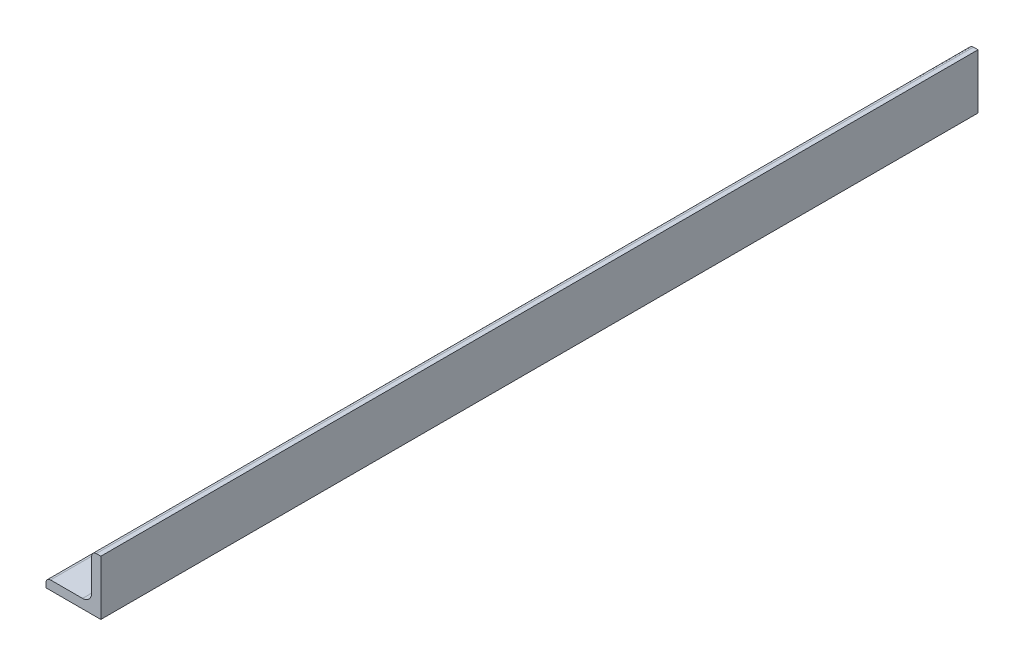
SolidWorks part; units mm, degrees
material "6061-T6 (SS)"
ref_plane "Front Plane" through (0, 0, 0) normal (0, 0, 1) x (1, 0, 0)
ref_plane "Top Plane" through (0, 0, 0) normal (0, 1, 0) x (1, 0, 0)
ref_plane "Right Plane" through (0, 0, 0) normal (1, 0, 0) x (0, 0, -1)
sketch "Sketch0" plane through (0, 0, 0) normal (0, 0, 1) x (1, 0, 0)
  line L0 (-9.525, -9.525) -> (9.525, -9.525)
  line L1 (9.525, -9.525) -> (9.525, 9.525)
  line L2 (9.525, 0) -> (0, 0) construction
  line L3 (0, 0) -> (0, -9.525) construction
  line L4 (6.35, -3.175) -> (6.35, 9.525) construction
  line L5 (3.175, -6.35) -> (-9.525, -6.35) construction
  arc A0 (6.35, -3.175) -> (3.175, -6.35) centre (3.175, -3.175) cw
  point P3 (5.4201, -5.4201)
  dimension "Inside Corner Radius" = 3.175
  dimension "Outside Height" = 19.05
  dimension "Inside Height" = 15.875
  dimension "Inside Width" = 15.875
  dimension "Wall Thickness" = 3.175
  dimension "D1" = 3.175
  dimension "Outside Width" = 19.05
sketch "Sketch1" plane through (0, 0, 0) normal (1, 0, 0) x (0, 0, -1)
  line L0 (152.4, 0) -> (-152.4, 0)
  point P4 (0, 0)
  dimension "Length" = 304.8
sketch "Sketch2" plane through (0, 0, 0) normal (0, 0, 1) x (1, 0, 0)
  line L0 (-9.525, -9.525) -> (9.525, -9.525)
  line L1 (9.525, -9.525) -> (9.525, 9.525)
  line L2 (9.525, 9.525) -> (6.35, 9.525) construction
  line L3 (6.35, 7.9375) -> (6.35, -3.175)
  line L4 (3.175, -6.35) -> (-7.9375, -6.35)
  line L5 (-9.525, -9.525) -> (-9.525, -6.35) construction
  line L6 (7.9375, 9.525) -> (9.525, 9.525)
  line L7 (-9.525, -7.9375) -> (-9.525, -9.525)
  line L8 (9.525, 0) -> (0, 0) construction
  line L9 (0, 0) -> (0, -9.525) construction
  arc A0 (6.35, 7.9375) -> (7.9375, 9.525) centre (7.9375, 7.9375) cw
  arc A1 (-9.525, -7.9375) -> (-7.9375, -6.35) centre (-7.9375, -7.9375) cw
  arc A2 (6.35, -3.175) -> (3.175, -6.35) centre (3.175, -3.175) cw
  dimension "Inside Radius" = 3.175
  dimension "Height" = 19.05
  dimension "Width" = 19.05
  dimension "Thickness" = 3.175
extrude "Boss-Extrude1" add sketch "Sketch2" along normal mid plane 304.8
sketch "Break Locations" plane through (0, 0, 0) normal (1, 0, 0) x (0, 0, -1)
  line L0 (-132.969, 0) -> (132.969, 0)
  line L1 (-152.4, -9.525) -> (-152.4, 9.525) construction
  line L2 (152.4, -9.525) -> (152.4, 9.525) construction
  point P0 (-136.2075, 0)
  point P1 (136.2075, 0)
  point P10 (0, 0)
  point P11 (132.969, 0)
  point P13 (-132.969, 0)
  dimension "D1" = 16.1925
  dimension "D2" = 16.1925
  dimension "D3" = 19.431
equation "\"D1@Break Locations\" = .85 * \"Height@Sketch2\""
equation "\"D2@Break Locations\"=\"D1@Break Locations\""
equation "\"Thickness@Sketch2\"=\"wall thickness@sketch0\""
equation "\"Height@Sketch2\"=\"outside height@sketch0\""
equation "\"Width@Sketch2\"=\"outside width@sketch0\""
equation "\"Inside Radius@Sketch2\"=\"inside corner radius@sketch0\""
equation "\"Length@Boss-Extrude1\"=\"length@sketch1\""
equation "\"D3@Break Locations\"=\"D2@Break Locations\"*1.2"
equation "\"D1@Sketch0\"=\"Wall Thickness@Sketch0\""
